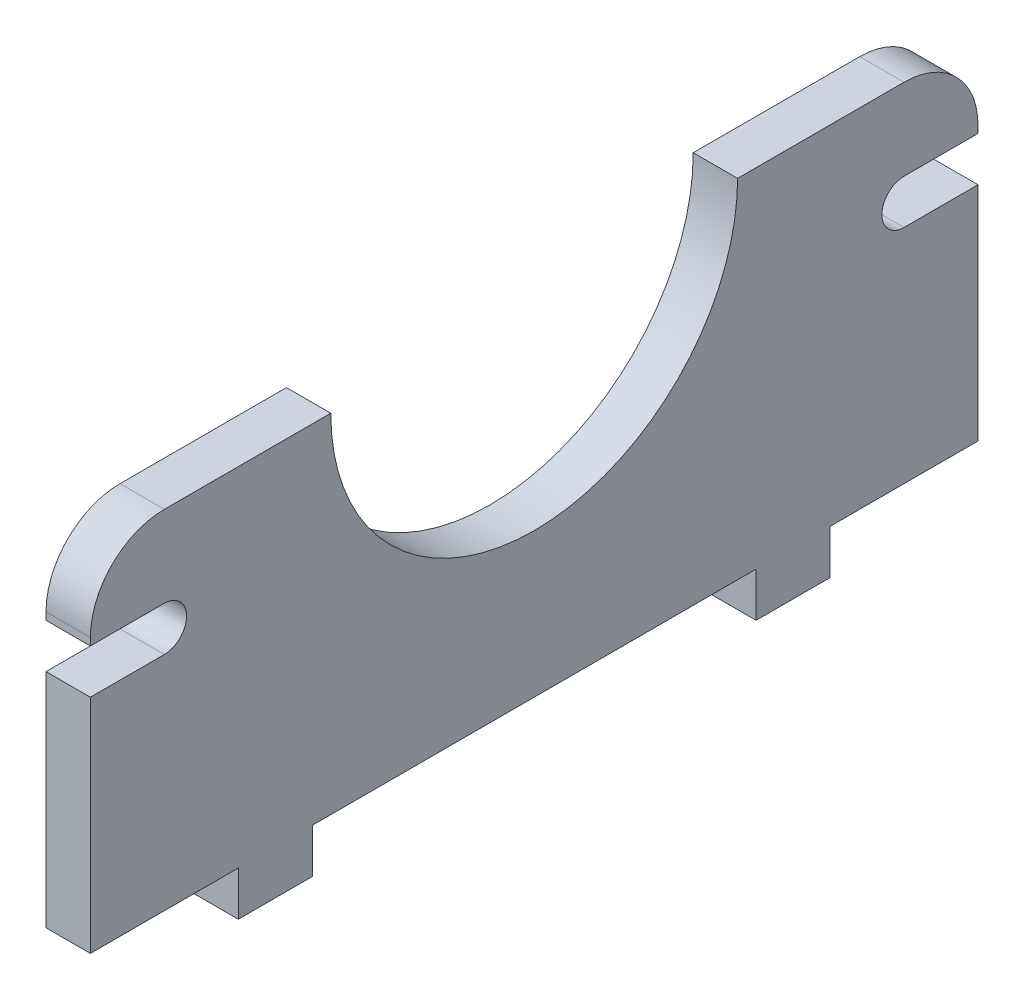
SolidWorks part; units mm, degrees
ref_plane "Front Plane" through (0, 0, 0) normal (0, 0, 1) x (1, 0, 0)
ref_plane "Top Plane" through (0, 0, 0) normal (0, 1, 0) x (1, 0, 0)
ref_plane "Right Plane" through (0, 0, 0) normal (1, 0, 0) x (0, 0, -1)
ref_plane "Plane1" through (0, -2, 0) normal (0, 1, 0) x (1, 0, 0)
sketch "Sketch1" plane through (0, 0, 0) normal (1, 0, 0) x (0, 0, -1)
  line L0 (-13.75, 11.75) -> (-30, 11.75)
  line L1 (30, -11.75) -> (-30, -11.75)
  line L2 (30, -11.75) -> (30, 11.75)
  line L3 (30, 11.75) -> (13.75, 11.75)
  line L4 (-30, -11.75) -> (-30, 11.75)
  line L5 (30, -11.75) -> (-30, 11.75) construction
  line L6 (30, 11.75) -> (-30, -11.75) construction
  arc A0 (-13.75, 11.75) -> (13.75, 11.75) centre (0, 11.75) ccw
  point P0 (0, 0)
  dimension "D4" = 27.5
  dimension "D2" = 60
  dimension "D3" = 23.5
extrude "Boss-Extrude1" add sketch "Sketch1" along normal blind 3
sketch "Sketch2" plane through (3, 0, 0) normal (1, 0, 0) x (0, 0, -1)
  line L5 (-30, 11.75) -> (-30, -11.75) construction
  line L6 (-25, 6.25) -> (-30, 6.25)
  line L9 (-25, 3.25) -> (-30, 3.25)
  line L10 (-30, 6.25) -> (-30, 3.25)
  line L11 (-30, -11.75) -> (30, -11.75) construction
  arc A0 (-25, 3.25) -> (-25, 6.25) centre (-25, 4.75) ccw
  point P0 (-13.5, -6.75)
  dimension "D1" = 3
  dimension "D2" = 15
  dimension "D3" = 5
extrude "Cut-Extrude1" cut sketch "Sketch2" against normal through all
mirror "Mirror2" about plane through (0, 0, 0) normal (0, 0, 1) of "Cut-Extrude1"
fillet "Fillet1" radius 5 2 edges at (1.5, 11.75, -30) (1.5, 11.75, 30)
sketch "Sketch3" plane through (0, -11.75, 0) normal (0, -1, 0) x (1, 0, 0)
  line L0 (3, 30) -> (3, -30) construction
  line L1 (3, 20) -> (0, 20)
  line L2 (3, 20) -> (3, 15)
  line L3 (3, 15) -> (0, 15)
  line L4 (0, 20) -> (0, 15)
  line L5 (0, 30) -> (0, -30) construction
  line L6 (3, 30) -> (0, 30) construction
  dimension "D1" = 10
  dimension "D2" = 5
extrude "Boss-Extrude2" add sketch "Sketch3" along normal blind 3
mirror "Mirror3" about plane through (0, 0, 0) normal (0, 0, 1) of "Boss-Extrude2"
